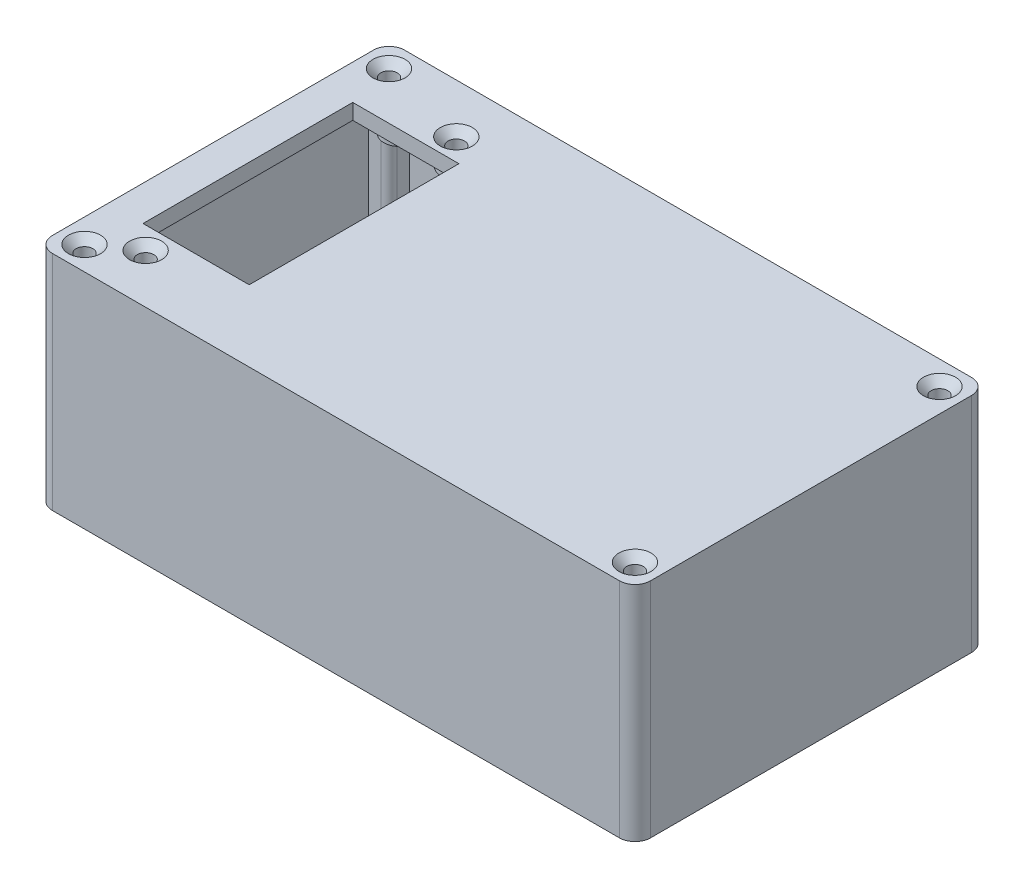
SolidWorks part; units mm, degrees
ref_plane "Спереди" through (0, 0, 0) normal (0, 0, 1) x (1, 0, 0)
ref_plane "Сверху" through (0, 0, 0) normal (0, 1, 0) x (1, 0, 0)
ref_plane "Справа" through (0, 0, 0) normal (1, 0, 0) x (0, 0, -1)
sketch "Эскиз3" plane through (0, 0, 0) normal (0, 1, 0) x (1, 0, 0)
  line L0 (-49.5717, 0) -> (69.7007, 0) construction
  line L1 (-17.7626, 27) -> (-37.7626, 27) construction
  line L2 (-17.7626, 27) -> (-17.7626, -27) construction
  line L3 (-17.7626, -27) -> (-37.7626, -27) construction
  line L4 (-37.7626, 27) -> (-37.7626, -27) construction
  line L5 (-17.7626, 27) -> (-37.7626, -27) construction
  line L6 (-17.7626, -27) -> (-37.7626, 27) construction
  line L7 (25.2374, -28.8528) -> (25.2374, 15.3477) construction
  line L8 (-9.7626, 25.5) -> (60.2374, 25.5) construction
  line L9 (-9.7626, 25.5) -> (-9.7626, -25.5) construction
  line L10 (-9.7626, -25.5) -> (60.2374, -25.5) construction
  line L11 (60.2374, 25.5) -> (60.2374, -25.5) construction
  line L12 (-9.7626, 25.5) -> (60.2374, -25.5) construction
  line L13 (-9.7626, -25.5) -> (60.2374, 25.5) construction
  line L14 (-14.2626, 20) -> (64.7374, 20) construction
  line L15 (-14.2626, 20) -> (-14.2626, -20) construction
  line L16 (-14.2626, -20) -> (64.7374, -20) construction
  line L17 (64.7374, 20) -> (64.7374, -20) construction
  line L18 (-14.2626, 20) -> (64.7374, -20) construction
  line L19 (-14.2626, -20) -> (64.7374, 20) construction
  line L20 (67.7374, -34) -> (-41.7626, -34)
  line L21 (70.7374, -31) -> (70.7374, 31)
  line L22 (67.7374, 34) -> (-41.7626, 34)
  line L23 (-44.7626, -31) -> (-44.7626, 31)
  line L24 (70.7374, -34) -> (-44.7626, 34) construction
  line L25 (70.7374, 34) -> (-44.7626, -34) construction
  line L26 (57.2374, 22) -> (-6.7626, 22) construction
  line L27 (57.2374, 22) -> (57.2374, -22) construction
  line L28 (57.2374, -22) -> (-6.7626, -22) construction
  line L29 (-6.7626, 22) -> (-6.7626, -22) construction
  line L30 (57.2374, 22) -> (-6.7626, -22) construction
  line L31 (57.2374, -22) -> (-6.7626, 22) construction
  arc A0 (70.7374, 31) -> (67.7374, 34) centre (67.7374, 31) ccw
  arc A2 (67.7374, -34) -> (70.7374, -31) centre (67.7374, -31) ccw
  arc A3 (-41.7626, -34) -> (-44.7626, -31) centre (-41.7626, -31) cw
  arc A4 (-41.7626, 34) -> (-44.7626, 31) centre (-41.7626, 31) ccw
  point P0 (-27.7626, 0)
  point P8 (25.2374, 0)
  point P13 (25.2374, 0)
  point P18 (12.9874, 0)
  point P31 (25.2374, 0)
  dimension "D8" = 7
  dimension "D9" = 7
  dimension "D10" = 6
  dimension "D11" = 3
  dimension "D1" = 54
  dimension "D2" = 20
  dimension "D3" = 70
  dimension "D4" = 51
  dimension "D5" = 40
  dimension "D6" = 79
  dimension "D7" = 3.5
  dimension "D12" = 64
  dimension "D13" = 44
extrude "Вытянуть-Тонкостенный2" add sketch "Эскиз3" along normal blind 40 thin
sketch "Эскиз5" plane through (0, 0, 0) normal (0, -1, 0) x (1, 0, 0)
  line L0 (-43.4986, 27) -> (-43.4986, 32.0269)
  line L1 (12.9874, -34) -> (12.9874, 34) construction
  line L2 (67.7374, -34) -> (-41.7626, -34) construction
  line L3 (-43.4986, 27) -> (-39.2626, 27)
  line L4 (-37.7626, 32.0269) -> (-37.7626, 28.5)
  line L5 (-43.4986, 32.0269) -> (-37.7626, 32.0269)
  line L6 (-41.7626, 34) -> (67.7374, 34) construction
  line L7 (70.7374, 0) -> (-44.7626, 0) construction
  line L8 (70.7374, 31) -> (70.7374, -31) construction
  line L9 (-44.7626, -31) -> (-44.7626, 31) construction
  line L10 (-43.4986, -32.0269) -> (-37.7626, -32.0269)
  line L11 (-37.7626, -32.0269) -> (-37.7626, -28.5)
  line L12 (-43.4986, -27) -> (-39.2626, -27)
  line L13 (-43.4986, -27) -> (-43.4986, -32.0269)
  line L14 (69.4735, -27) -> (69.4735, -32.0269)
  line L15 (69.4735, -27) -> (65.2374, -27)
  line L16 (63.7374, -32.0269) -> (63.7374, -28.5)
  line L17 (69.4735, -32.0269) -> (63.7374, -32.0269)
  line L18 (69.4735, 32.0269) -> (63.7374, 32.0269)
  line L19 (63.7374, 32.0269) -> (63.7374, 28.5)
  line L20 (69.4735, 27) -> (65.2374, 27)
  line L21 (69.4735, 27) -> (69.4735, 32.0269)
  circle A0 centre (-40.1626, 29.4) radius 1.6
  arc A1 (-39.2626, 27) -> (-37.7626, 28.5) centre (-39.2626, 28.5) ccw
  arc A2 (-39.2626, -27) -> (-37.7626, -28.5) centre (-39.2626, -28.5) cw
  circle A3 centre (-40.1626, -29.4) radius 1.6
  circle A4 centre (66.1374, -29.4) radius 1.6
  arc A5 (65.2374, -27) -> (63.7374, -28.5) centre (65.2374, -28.5) ccw
  arc A6 (65.2374, 27) -> (63.7374, 28.5) centre (65.2374, 28.5) cw
  circle A7 centre (66.1374, 29.4) radius 1.6
  dimension "D3" = 3.2
  dimension "D1" = 1.5
  dimension "D4" = 2.4
  dimension "D5" = 2.4
extrude "Бобышка-Вытянуть2" add sketch "Эскиз5" against normal up to surface (40 mm away) up to face at (12.9874, 40, 0)
sketch "Эскиз7" plane through (0, 40, 0) normal (0, 1, 0) x (1, 0, 0)
  line L0 (67.7374, 34) -> (-41.7626, 34) construction
  line L1 (-44.7626, 31) -> (-44.7626, -31) construction
  line L2 (-41.7626, -34) -> (67.7374, -34) construction
  line L3 (70.7374, -31) -> (70.7374, 31) construction
  line L4 (70.7374, -31) -> (70.7374, 31)
  line L5 (-41.7626, -34) -> (67.7374, -34)
  line L6 (-44.7626, 31) -> (-44.7626, -31)
  line L7 (67.7374, 34) -> (-41.7626, 34)
  arc A0 (-41.7626, 34) -> (-44.7626, 31) centre (-41.7626, 31) ccw construction
  circle A1 centre (-40.1626, 29.4) radius 1.6 construction
  circle A2 centre (-40.1626, -29.4) radius 1.6 construction
  arc A3 (-44.7626, -31) -> (-41.7626, -34) centre (-41.7626, -31) ccw construction
  arc A4 (67.7374, -34) -> (70.7374, -31) centre (67.7374, -31) ccw construction
  circle A5 centre (66.1374, -29.4) radius 1.6 construction
  arc A6 (70.7374, 31) -> (67.7374, 34) centre (67.7374, 31) ccw construction
  circle A7 centre (66.1374, 29.4) radius 1.6 construction
  circle A8 centre (66.1374, 29.4) radius 1.6
  arc A9 (70.7374, 31) -> (67.7374, 34) centre (67.7374, 31) ccw
  circle A10 centre (66.1374, -29.4) radius 1.6
  arc A11 (67.7374, -34) -> (70.7374, -31) centre (67.7374, -31) ccw
  arc A12 (-44.7626, -31) -> (-41.7626, -34) centre (-41.7626, -31) ccw
  circle A13 centre (-40.1626, -29.4) radius 1.6
  circle A14 centre (-40.1626, 29.4) radius 1.6
  arc A15 (-41.7626, 34) -> (-44.7626, 31) centre (-41.7626, 31) ccw
extrude "Бобышка-Вытянуть3" add sketch "Эскиз7" along normal blind 3
chamfer "Фаска1" distance 1.5 angle 45 4 edges at (66.1374, 43, -27.8) (66.1374, 43, 31) (-40.1626, 43, 31) (-40.1626, 43, -27.8)
sketch "Эскиз9" plane through (0, 40, 0) normal (0, -1, 0) x (1, 0, 0)
  line L33 (-49.5717, 0) -> (69.7007, 0) construction
  line L34 (-17.7626, 27) -> (-37.7626, 27) construction
  line L35 (-17.7626, 27) -> (-17.7626, -27) construction
  line L36 (-17.7626, -27) -> (-37.7626, -27) construction
  line L37 (-37.7626, 27) -> (-37.7626, -27) construction
  line L38 (-17.7626, 27) -> (-37.7626, -27) construction
  line L39 (-17.7626, -27) -> (-37.7626, 27) construction
  line L40 (25.2374, -28.8528) -> (25.2374, 15.3477) construction
  line L41 (-9.5223, 25.5) -> (59.9972, 25.5) construction
  line L42 (-9.5223, 25.5) -> (-9.5223, -25.5) construction
  line L43 (-9.5223, -25.5) -> (59.9972, -25.5) construction
  line L44 (59.9972, 25.5) -> (59.9972, -25.5) construction
  line L45 (-9.5223, 25.5) -> (59.9972, -25.5) construction
  line L46 (-9.5223, -25.5) -> (59.9972, 25.5) construction
  line L47 (-14.2626, 20.3539) -> (64.7374, 20.3539) construction
  line L48 (-14.2626, 20.3539) -> (-14.2626, -20.3539) construction
  line L49 (-14.2626, -20.3539) -> (64.7374, -20.3539) construction
  line L50 (64.7374, 20.3539) -> (64.7374, -20.3539) construction
  line L51 (-14.2626, 20.3539) -> (64.7374, -20.3539) construction
  line L52 (-14.2626, -20.3539) -> (64.7374, 20.3539) construction
  line L53 (67.7374, -34) -> (-41.7626, -34)
  line L54 (70.7374, -31) -> (70.7374, 31)
  line L55 (67.7374, 34) -> (-41.7626, 34)
  line L56 (-44.7626, -31) -> (-44.7626, 31)
  line L57 (70.7374, -34) -> (-44.7626, 34) construction
  line L58 (70.7374, 34) -> (-44.7626, -34) construction
  line L59 (57.2374, 22) -> (-6.7626, 22) construction
  line L60 (57.2374, 22) -> (57.2374, -22) construction
  line L61 (57.2374, -22) -> (-6.7626, -22) construction
  line L62 (-6.7626, 22) -> (-6.7626, -22) construction
  line L63 (57.2374, 22) -> (-6.7626, -22) construction
  line L64 (57.2374, -22) -> (-6.7626, 22) construction
  circle A0 centre (-6.7626, 22) radius 0.75
  circle A1 centre (-6.7626, 22) radius 3
  circle A2 centre (57.2374, 22) radius 3
  circle A3 centre (57.2374, 22) radius 0.75
  arc A4 (70.7374, 31) -> (67.7374, 34) centre (67.7374, 31) ccw
  arc A5 (67.7374, -34) -> (70.7374, -31) centre (67.7374, -31) ccw
  arc A6 (-41.7626, -34) -> (-44.7626, -31) centre (-41.7626, -31) cw
  arc A7 (-41.7626, 34) -> (-44.7626, 31) centre (-41.7626, 31) ccw
  circle A8 centre (57.2374, -22) radius 0.75
  circle A9 centre (57.2374, -22) radius 3
  circle A10 centre (-6.7626, -22) radius 3
  circle A11 centre (-6.7626, -22) radius 0.75
  point P44 (-27.7626, 0)
  point P51 (25.2374, 0)
  point P56 (25.2374, 0)
  point P61 (12.9874, 0)
  point P74 (25.2374, 0)
  dimension "D12" = 3
  dimension "D2" = 1.5
  dimension "D3" = 6
  dimension "D8" = 51
  dimension "D9" = 3.5
  dimension "D10" = 7
  dimension "D11" = 6
extrude "Бобышка-Вытянуть4" add sketch "Эскиз9" along normal blind 3 contours A1 A0 | A2 A3 | A9 A8 | A10 A11
sketch "Эскиз10" plane through (0, 40, 0) normal (0, -1, 0) x (1, 0, 0)
  line L0 (-49.5717, 0) -> (69.7007, 0) construction
  line L1 (-17.7626, 27) -> (-37.7626, 27) construction
  line L2 (-17.7626, 27) -> (-17.7626, -27) construction
  line L3 (-17.7626, -27) -> (-37.7626, -27) construction
  line L4 (-37.7626, 27) -> (-37.7626, -27) construction
  line L5 (-17.7626, 27) -> (-37.7626, -27) construction
  line L6 (-17.7626, -27) -> (-37.7626, 27) construction
  line L7 (25.2374, -28.8528) -> (25.2374, 15.3477) construction
  line L8 (-9.7626, 25.5) -> (60.2374, 25.5) construction
  line L9 (-9.7626, 25.5) -> (-9.7626, -25.5) construction
  line L10 (-9.7626, -25.5) -> (60.2374, -25.5) construction
  line L11 (60.2374, 25.5) -> (60.2374, -25.5) construction
  line L12 (-9.7626, 25.5) -> (60.2374, -25.5) construction
  line L13 (-9.7626, -25.5) -> (60.2374, 25.5) construction
  line L14 (-14.2626, 28.8979) -> (64.7374, 28.8979) construction
  line L15 (-14.2626, 28.8979) -> (-14.2626, -28.8979) construction
  line L19 (-14.2626, -28.8979) -> (64.7374, 28.8979) construction
  line L25 (70.7374, 34) -> (-44.7626, -34) construction
  line L26 (57.2374, 22) -> (-6.7626, 22) construction
  line L27 (57.2374, 22) -> (57.2374, -22) construction
  line L28 (57.2374, -22) -> (-6.7626, -22) construction
  line L29 (-6.7626, 22) -> (-6.7626, -22) construction
  line L30 (57.2374, 22) -> (-6.7626, -22) construction
  line L31 (57.2374, -22) -> (-6.7626, 22) construction
  line L33 (-22.2626, -24.5) -> (-33.2626, -24.5) construction
  line L34 (-22.2626, -24.5) -> (-22.2626, 24.5) construction
  line L35 (-22.2626, 24.5) -> (-33.2626, 24.5) construction
  line L36 (-33.2626, -24.5) -> (-33.2626, 24.5) construction
  line L37 (-22.2626, -24.5) -> (-33.2626, 24.5) construction
  line L38 (-22.2626, 24.5) -> (-33.2626, -24.5) construction
  line L39 (-17.5126, -20.25) -> (-38.0126, -20.25)
  line L40 (-17.5126, -20.25) -> (-17.5126, 20.25)
  line L41 (-17.5126, 20.25) -> (-38.0126, 20.25)
  line L42 (-38.0126, -20.25) -> (-38.0126, 20.25)
  line L43 (-17.5126, -20.25) -> (-38.0126, 20.25) construction
  line L44 (-17.5126, 20.25) -> (-38.0126, -20.25) construction
  circle A4 centre (-33.2626, 24.5) radius 1.6
  circle A5 centre (-22.2626, -24.5) radius 1.6
  point P0 (12.9874, 0)
  point P1 (-27.7626, 0)
  point P3 (-27.7626, 0)
  point P10 (25.2374, 0)
  point P15 (25.2374, 0)
  point P20 (12.9874, 0)
  point P33 (25.2374, 0)
  point P49 (-27.7626, 0)
  dimension "D8" = 3.2
  dimension "D9" = 3.2
  dimension "D2" = 3.5
  dimension "D6" = 11
  dimension "D7" = 49
  dimension "D10" = 40.5
  dimension "D11" = 20.5
extrude "Вырез-Вытянуть1" cut sketch "Эскиз10" against normal through all
chamfer "Фаска2" distance 1.5 angle 45 2 edges at (-22.2626, 43, -26.1) (-33.2626, 43, 22.9)
fillet "Скругление2" radius 1.5 1 edges at (12.9874, 40, 31)
fillet "Скругление3" radius 1.5 3 edges at (67.7374, 40, 0) (12.9874, 40, -31) (-41.7626, 40, 0)
sketch "Эскиз12" plane through (0, 40, 0) normal (0, -1, 0) x (1, 0, 0)
  line L0 (-27.7626, 20.25) -> (-27.7626, -20.25) construction
  line L1 (-17.5126, 20.25) -> (-38.0126, 20.25) construction
  line L2 (-38.0126, -20.25) -> (-17.5126, -20.25) construction
  circle A0 centre (-33.2626, 24.5) radius 1.6
  circle A1 centre (-33.2626, 24.5) radius 3
  circle A2 centre (-22.2626, -24.5) radius 1.6
  circle A3 centre (-22.2626, -24.5) radius 3
  circle A4 centre (-33.2626, -24.5) radius 3
  circle A5 centre (-22.2626, 24.5) radius 3
  dimension "D1" = 6
  dimension "D2" = 6
extrude "Бобышка-Вытянуть5" add sketch "Эскиз12" along normal blind 2
